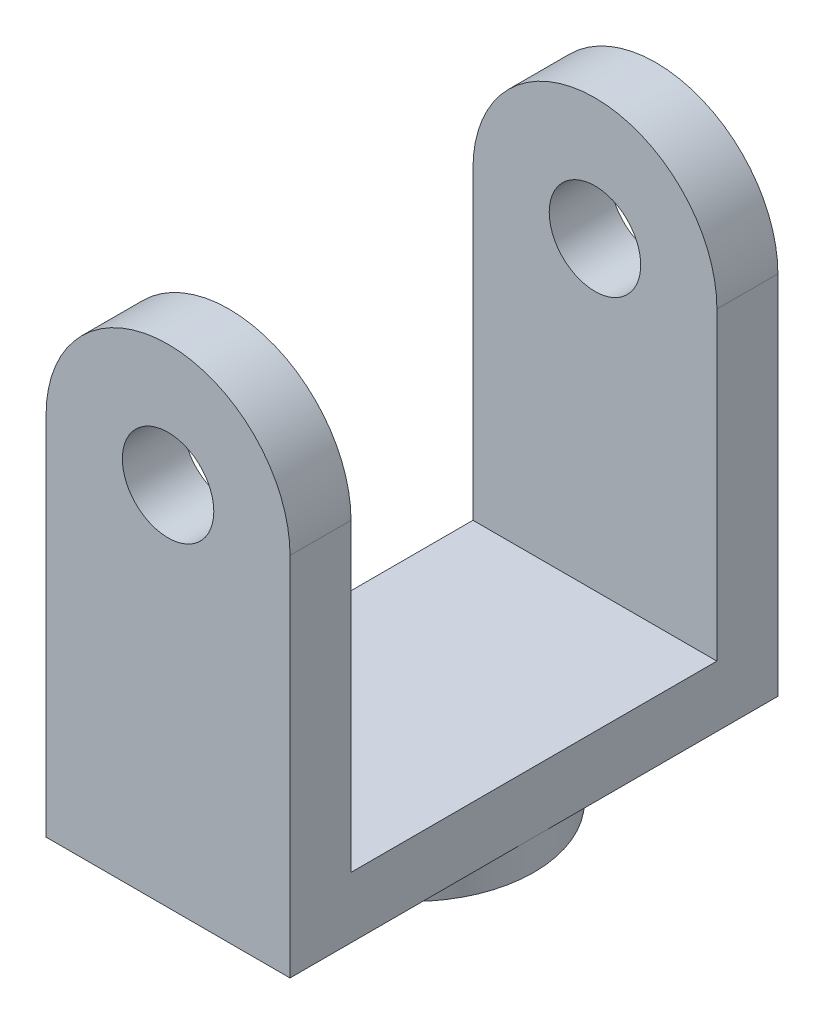
SolidWorks part; units mm, degrees
ref_plane "Front Plane" through (0, 0, 0) normal (0, 0, 1) x (1, 0, 0)
ref_plane "Top Plane" through (0, 0, 0) normal (0, 1, 0) x (1, 0, 0)
ref_plane "Right Plane" through (0, 0, 0) normal (1, 0, 0) x (0, 0, -1)
sketch "Sketch1" plane through (0, 0, 0) normal (0, 0, 1) x (1, 0, 0)
  line L0 (-25.4, 0) -> (-25.4, -76.2)
  line L1 (-25.4, -76.2) -> (25.4, -76.2)
  line L2 (25.4, -76.2) -> (25.4, 0)
  circle A0 centre (0, 0) radius 9.525
  arc A1 (25.4, 0) -> (-25.4, 0) centre (0, 0) ccw
  arc A2 (-25.4, 0) -> (25.4, 0) centre (0, 0) ccw construction
  dimension "D1" = 19.05
  dimension "D2" = 50.8
  dimension "D3" = 76.2
extrude "Boss-Extrude1" add sketch "Sketch1" along normal mid plane 101.6
sketch "Sketch2" plane through (0, 0, 0) normal (1, 0, 0) x (0, 0, -1)
  line L1 (-38.1, -63.5) -> (38.1, -63.5)
  line L2 (-38.1, -63.5) -> (-38.1, 25.4)
  line L3 (-38.1, 25.4) -> (38.1, 25.4)
  line L4 (38.1, -63.5) -> (38.1, 25.4)
  line L5 (50.8, 25.4) -> (-50.8, 25.4) construction
  point P4 (0, 25.4)
  dimension "D1" = 76.2
  dimension "D2" = 63.5
extrude "Cut-Extrude1" cut sketch "Sketch2" against normal through all both and the other way through all
sketch "Sketch3" plane through (0, -76.2, 0) normal (0, -1, 0) x (1, 0, 0)
  circle A0 centre (0, 0) radius 25.4
  dimension "D1" = 50.8
extrude "Boss-Extrude2" add sketch "Sketch3" along normal blind 6.35
